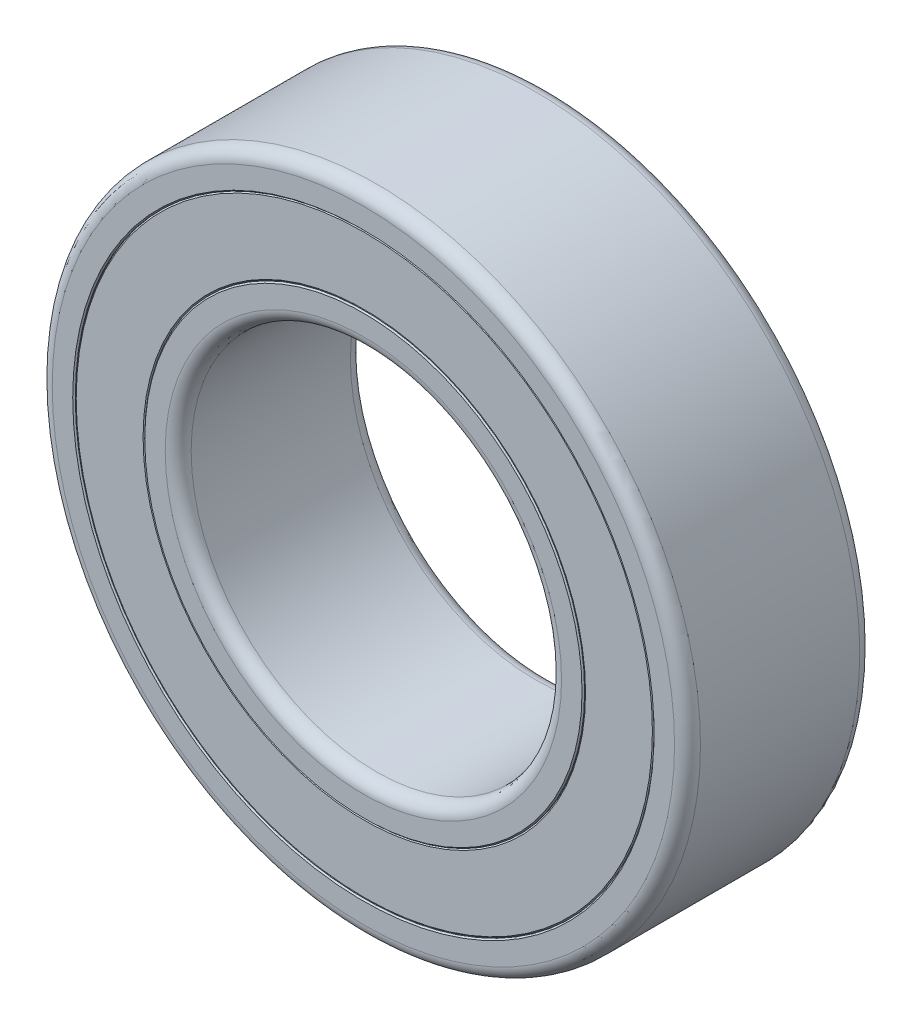
SolidWorks part; units mm, degrees
material "AISI 316 Annealed Stainless Steel Bar (SS)"
ref_plane "Front" through (0, 0, 0) normal (0, 0, 1) x (1, 0, 0)
ref_plane "Top" through (0, 0, 0) normal (0, 1, 0) x (1, 0, 0)
ref_plane "Right" through (0, 0, 0) normal (1, 0, 0) x (0, 0, -1)
sketch "LAYOUT R" plane through (0, 0, 0) normal (1, 0, 0) x (0, 0, -1)
  line L0 (-2, 4) -> (2, 4)
  line L1 (2, -7) -> (-2, -7) construction
  line L2 (2, -7) -> (2, 7) construction
  line L3 (2, 7) -> (-2, 7)
  line L4 (-2, -7) -> (-2, 7) construction
  line L5 (2, -7) -> (-2, 7) construction
  line L6 (2, 7) -> (-2, -7) construction
  line L7 (-2, 4.75) -> (2, 4.75)
  line L8 (-2, 6.25) -> (2, 6.25)
  line L11 (-17.5, 0) -> (17.5, 0) construction
  line L12 (-2, 7) -> (-2, 6.25)
  line L13 (2, 7) -> (2, 6.25)
  line L14 (-2, 6.25) -> (-2, 4.75)
  line L15 (2, 6.25) -> (2, 4.75)
  line L16 (-2, 4.75) -> (-2, 4)
  line L17 (2, 4.75) -> (2, 4)
  line L18 (-1.98, 6.25) -> (-1.98, 4.75)
  line L19 (1.98, 6.25) -> (1.98, 4.75)
  point P0 (0, 0)
  point P15 (0, 0)
  dimension "D1" = 4
  dimension "D2" = 14
  dimension "D3" = 4
  dimension "D6" = 0.02
  dimension "D7" = 0.02
  dimension "D4" = 4.75
  dimension "D5" = 6.25
sketch "Sketch R, INNER BODY" plane through (0, 0, 0) normal (1, 0, 0) x (0, 0, -1)
  line L0 (-2, 4) -> (2, 4) construction
  line L2 (-2, 4.75) -> (2, 4.75) construction
  line L4 (-2, 4) -> (2, 4)
  line L6 (-2, 4.75) -> (2, 4.75)
  line L8 (2, 4.75) -> (2, 4) construction
  line L9 (-2, 4.75) -> (-2, 4) construction
  line L10 (2, 4.75) -> (2, 4)
  line L11 (-2, 4.75) -> (-2, 4)
  line L12 (-17.5, 0) -> (17.5, 0) construction
  line L13 (-17.5, 0) -> (17.5, 0) construction
sketch "Sketch R, OUTER BODY" plane through (0, 0, 0) normal (1, 0, 0) x (0, 0, -1)
  line L2 (-2, 6.25) -> (2, 6.25) construction
  line L3 (2, 7) -> (-2, 7) construction
  line L6 (-2, 6.25) -> (2, 6.25)
  line L7 (2, 7) -> (-2, 7)
  line L8 (-17.5, 0) -> (17.5, 0) construction
  line L9 (-17.5, 0) -> (17.5, 0) construction
  line L10 (2, 7) -> (2, 6.25) construction
  line L11 (-2, 7) -> (-2, 6.25) construction
  line L12 (2, 7) -> (2, 6.25)
  line L13 (-2, 7) -> (-2, 6.25)
sketch "Sketch R, SEAL FACES" plane through (0, 0, 0) normal (1, 0, 0) x (0, 0, -1)
  line L0 (-17.5, 0) -> (17.5, 0) construction
  line L1 (-17.5, 0) -> (17.5, 0) construction
  line L3 (-2, 4.75) -> (2, 4.75) construction
  line L5 (-2, 6.25) -> (2, 6.25) construction
  line L7 (-1.98, 4.75) -> (1.98, 4.75)
  line L9 (-1.98, 6.25) -> (1.98, 6.25)
  line L10 (1.98, 6.25) -> (1.98, 4.75) construction
  line L11 (-1.98, 6.25) -> (-1.98, 4.75) construction
  line L12 (1.98, 6.25) -> (1.98, 4.75)
  line L13 (-1.98, 6.25) -> (-1.98, 4.75)
revolve "Revolve INNER BODY" add sketch "Sketch R, INNER BODY" angle 360 about L13
fillet "Fillet INNER BODY" radius 0.28 2 edges at (4, 0, 2) (4, 0, -2)
chamfer "Chamfer INNER BODY" distance 0.028 angle 45 2 edges at (4.75, 0, -2) (4.75, 0, 2)
revolve "Revolve OUTER BODY" add sketch "Sketch R, OUTER BODY" angle 360 about L9
fillet "Fillet OUTER BODY" radius 0.28 2 edges at (7, 0, -2) (7, 0, 2)
chamfer "Chamfer OUTER BODY" distance 0.028 angle 45 2 edges at (6.25, 0, 2) (6.25, 0, -2)
revolve "Revolve SEALS" add sketch "Sketch R, SEAL FACES" angle 360 about L1
chamfer "Chamfer SEALS" distance 0.028 angle 45 4 edges at (4.75, 0, -1.98) (6.25, 0, -1.98) (6.25, 0, 1.98) (4.75, 0, 1.98)
sketch "Sketch TEXT RADIUS 1 — MANUALLY ASSIGN TEXT AND FONT SIZE (FROM EQUATIONS)" [suppressed] plane through (0, 0, 1.98) normal (0, 0, 1) x (1, 0, 0)
  circle A0 centre (0, 0) radius 5.275 construction
  text T0 "MR148-2RS  8x14x3.5mm" font "Century Gothic" height 0.45
  dimension "D1" = 10.55
extrude "Cut-Extrude SEAL LABEL 1" [suppressed] cut sketch "Sketch TEXT RADIUS 1 — MANUALLY ASSIGN TEXT AND FONT SIZE (FROM EQUATIONS)" against normal blind 0.05
sketch "Sketch TEXT RADIUS 2 — MANUALLY ASSIGN TEXT AND FONT SIZE (FROM EQUATIONS)" [suppressed] plane through (0, 0, -1.98) normal (0, 0, -1) x (-1, 0, 0)
  circle A0 centre (0, 0) radius 5.275 construction
  text T0 "MR148-2RS  8x14x3.5mm" font "Century Gothic" height 0.45
  dimension "D1" = 10.55
extrude "Cut-Extrude SEAL LABEL 2" [suppressed] cut sketch "Sketch TEXT RADIUS 2 — MANUALLY ASSIGN TEXT AND FONT SIZE (FROM EQUATIONS)" against normal blind 0.05
sketch "Sketch1" plane through (0, 0, -1.98) normal (0, 0, -1) x (-1, 0, 0)
  circle A1 centre (0, 0) radius 6.222
  circle A2 centre (0, 0) radius 6.222
  dimension "D1" = 0
equation "\"_i__BORE\"= 8"
equation "\"_i__OUTSIDE_DIAMETER\"= 14"
equation "\"_i__WIDTH\"= 4.0"
equation "\"_i_optional__TEXT_RADIUS_ADJUSTMENT\"= 0"
equation "\"_output__FONT_SIZE_mm\"= \"BODY_SPAN__SEAL__OF_RADIUS\" * \"param__FONT_SIZE_RATIO\"'MANUALLY ASSIGN TO FONT"
equation "\"BODY__HALF_WIDTH\"= \"_i__WIDTH\" / 2"
equation "\"BODY_SPAN___OF_DIAMETER\"= \"_i__OUTSIDE_DIAMETER\" - \"_i__BORE\""
equation "\"BODY_SPAN___OF_RADIUS\"= \"BODY_SPAN___OF_DIAMETER\" / 2"
equation "\"BODY_SPAN__BORE_AND_OD__OF RADIUS\"= ( \"BODY_SPAN___OF_RADIUS\" - \"BODY_SPAN__SEAL__OF_RADIUS\" ) / 2"
equation "\"BODY_SPAN__SEAL__OF_RADIUS\"= \"BODY_SPAN___OF_RADIUS\" * \"param__SEAL_PANEL_SPAN__RATIO_OF_BODY_RADIAN\""
equation "\"BORE__RADIUS\"= \"_i__BORE\" / 2"
equation "\"CORNER_RADII\"= \"_i__WIDTH\" * \"param__CORNER_RADII__ISO_MAX_RATIO_TO_WIDTH\""
equation "\"param__CORNER_RADII__ISO_MAX_RATIO_TO_WIDTH\"= 0.07'WHERE WIDTH IS LESS THAN DIAMETER"
equation "\"param__FONT_SIZE_RATIO\"= 0.3"
equation "\"param__SEAL_FACE_INSET__RATIO_OF_WIDTH\"= .01"
equation "\"param__SEAL_PANEL_SPAN__RATIO_OF_BODY_RADIAN\"= 0.5"
equation "\"param__SIDE_CHAMFERS__RATIO_TO_OD\"= 1 / 500"
equation "\"RING_INNER__OUTSIDE_RADIUS\"= \"BORE__RADIUS\" + \"BODY_SPAN__BORE_AND_OD__OF RADIUS\""
equation "\"RING_OUTER__OUTSIDE_RADIUS\"= ( \"_i__OUTSIDE_DIAMETER\" / 2 ) - \"BODY_SPAN__BORE_AND_OD__OF RADIUS\""
equation "\"SEAL_FACE_INSET\"= \"_i__WIDTH\" * \"param__SEAL_FACE_INSET__RATIO_OF_WIDTH\""
equation "\"SIDE_FACE_AND_SEAL_CHAMFERS\"= \"_i__OUTSIDE_DIAMETER\" * \"param__SIDE_CHAMFERS__RATIO_TO_OD\""
equation "\"TEXT_RADIUS\"= \"_i__BORE\" + ( \"BODY_SPAN___OF_DIAMETER\" / 2 ) - \"_output__FONT_SIZE_mm\" + \"_i_optional__TEXT_RADIUS_ADJUSTMENT\""
equation "\"D1@Chamfer INNER BODY\"=\"SIDE_FACE_AND_SEAL_CHAMFERS\""
equation "\"D1@Chamfer OUTER BODY\"=\"SIDE_FACE_AND_SEAL_CHAMFERS\""
equation "\"D1@Chamfer SEALS\"=\"SIDE_FACE_AND_SEAL_CHAMFERS\""
equation "\"D1@Fillet INNER BODY\"=\"CORNER_RADII\""
equation "\"D1@Fillet OUTER BODY\"=\"CORNER_RADII\""
equation "\"D1@LAYOUT R\"=\"_i__WIDTH\""
equation "\"D1@Sketch TEXT RADIUS 1 — MANUALLY ASSIGN TEXT AND FONT SIZE (FROM EQUATIONS)\" = \"TEXT_RADIUS\""
equation "\"D1@Sketch TEXT RADIUS 2 — MANUALLY ASSIGN TEXT AND FONT SIZE (FROM EQUATIONS)\" = \"TEXT_RADIUS\""
equation "\"D2@LAYOUT R\"=\"_i__OUTSIDE_DIAMETER\""
equation "\"D3@LAYOUT R\"=\"BORE__RADIUS\""
equation "\"D4@LAYOUT R\"=\"RING_INNER__OUTSIDE_RADIUS\""
equation "\"D5@LAYOUT R\"=\"RING_OUTER__OUTSIDE_RADIUS\""
